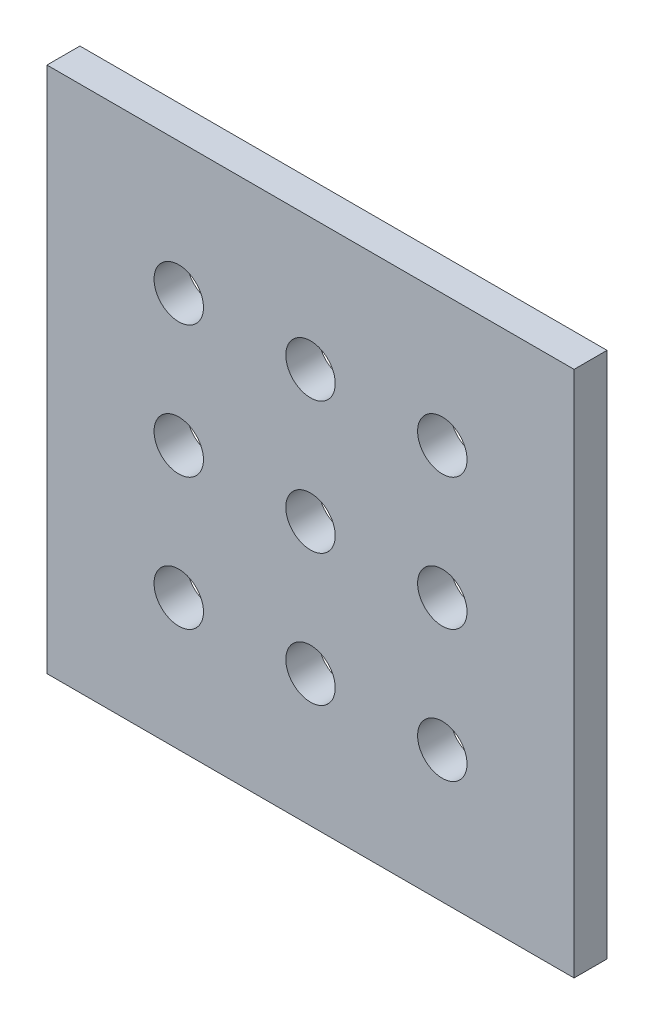
SolidWorks part; units mm, degrees
ref_plane "Front Plane" through (0, 0, 0) normal (0, 0, 1) x (1, 0, 0)
ref_plane "Top Plane" through (0, 0, 0) normal (0, 1, 0) x (1, 0, 0)
ref_plane "Right Plane" through (0, 0, 0) normal (1, 0, 0) x (0, 0, -1)
sketch "Sketch1" plane through (0, 0, 0) normal (0, 0, 1) x (1, 0, 0)
  line L1 (0, 0) -> (-50.8, 0)
  line L2 (0, 0) -> (0, 50.8)
  line L3 (0, 50.8) -> (-50.8, 50.8)
  line L4 (-50.8, 0) -> (-50.8, 50.8)
  circle A0 centre (-12.7, 12.7) radius 2.3813
  circle A1 centre (-25.4, 12.7) radius 2.3812
  circle A2 centre (-38.1, 12.7) radius 2.3812
  circle A3 centre (-25.4, 25.4) radius 2.3812
  circle A4 centre (-38.1, 25.4) radius 2.3812
  circle A5 centre (-25.4, 38.1) radius 2.3813
  circle A6 centre (-38.1, 38.1) radius 2.3812
  circle A11 centre (-12.7, 25.4) radius 2.3813
  circle A12 centre (-12.7, 38.1) radius 2.3812
  point P7 (-26.8242, 25.3199)
  dimension "D3" = 4.7625
  dimension "D1" = 12.7
  dimension "D2" = 12.7
  dimension "D6" = 12.7
  dimension "D7" = 12.7
  dimension "D8" = 12.7
  dimension "D9" = 12.7
  dimension "D4" = 3
  dimension "D5" = 3
extrude "Boss-Extrude1" add sketch "Sketch1" along normal blind 3.175
